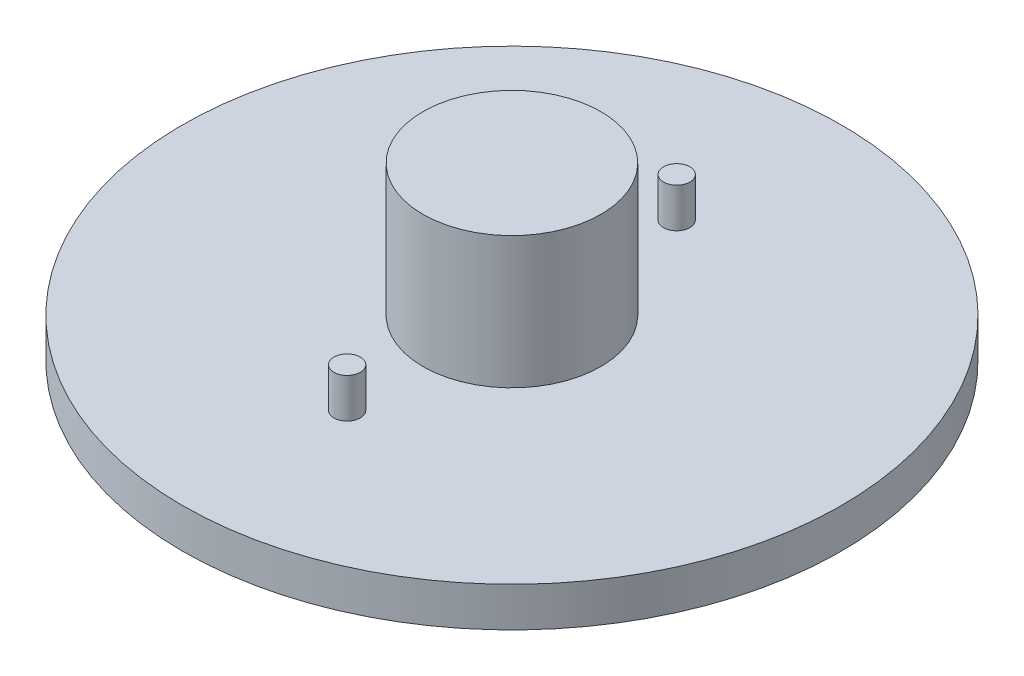
SolidWorks part; units mm, degrees
ref_plane "Plan de face" through (0, 0, 0) normal (0, 0, 1) x (1, 0, 0)
ref_plane "Plan de dessus" through (0, 0, 0) normal (0, 1, 0) x (1, 0, 0)
ref_plane "Plan de droite" through (0, 0, 0) normal (1, 0, 0) x (0, 0, -1)
sketch "Esquisse1" plane through (0, 0, 0) normal (0, 0, 1) x (1, 0, 0)
  line L0 (-5.6186, -7.2712) -> (35.8814, -7.2712)
  line L1 (35.8814, -7.2712) -> (35.8814, -1.2712)
  line L2 (35.8814, -1.2712) -> (-0.6186, -1.2712)
  line L3 (-0.6186, -1.2712) -> (-0.6186, 18.7288)
  line L4 (-0.6186, 18.7288) -> (-14.1186, 18.7288)
  line L5 (-14.1186, 18.7288) -> (-14.1186, 14.0817)
  line L6 (-14.1186, 14.0817) -> (-5.6186, 14.0817)
  line L7 (-5.6186, 14.0817) -> (-5.6186, -7.2712)
  dimension "D1" = 6
  dimension "D2" = 50
  dimension "D3" = 13.5
  dimension "D4" = 8.5
  dimension "D5" = 20
  dimension "D6" = 21.3529
revolve "Révolution4" add sketch "Esquisse1" angle 360 about L5
sketch "Esquisse2" plane through (0, -1.2712, 0) normal (0, 1, 0) x (1, 0, 0)
  line L0 (-14.1186, -13.5) -> (-14.1186, -59.0964) construction
  line L1 (-14.1186, -13.5) -> (-14.1186, 41.8826) construction
  line L2 (-14.1186, 0) -> (-68.3163, 0) construction
  circle A0 centre (-14.1186, 0) radius 13.5 construction
  circle A1 centre (-14.1186, -25) radius 2
  circle A2 centre (-14.1186, 25) radius 2
  point P8 (-14.1186, -25)
  dimension "D2" = 4
  dimension "D1" = 25
  dimension "D3" = 25
extrude "Boss.-Extru.1" add sketch "Esquisse2" along normal blind 6
sketch "Esquisse3" plane through (0, -7.2712, 0) normal (0, -1, 0) x (1, 0, 0)
  line L0 (-7.6186, 0) -> (-22.6186, 0) construction
  line L1 (-4.8422, 0) -> (-5.6186, 0)
  line L2 (-7.6186, 0) -> (-7.6186, -24.3656)
  line L3 (-7.6186, -24.3656) -> (-4.8422, -24.3656)
  line L4 (-4.8422, -24.3656) -> (-4.8422, 17.3314)
  line L5 (-4.8422, 17.3314) -> (-7.6186, 17.3314)
  line L6 (-7.6186, 17.3314) -> (-7.6186, 0)
  circle A0 centre (-14.1186, 0) radius 8.5 construction
  point P1 (-14.1186, -8.5)
  circle M2 centre (-14.1186, 0) radius 8.5
  dimension "D1" = 2
extrude "Boss.-Extru.2" add sketch "Esquisse3" against normal blind 25 contours L6 L2 M2
